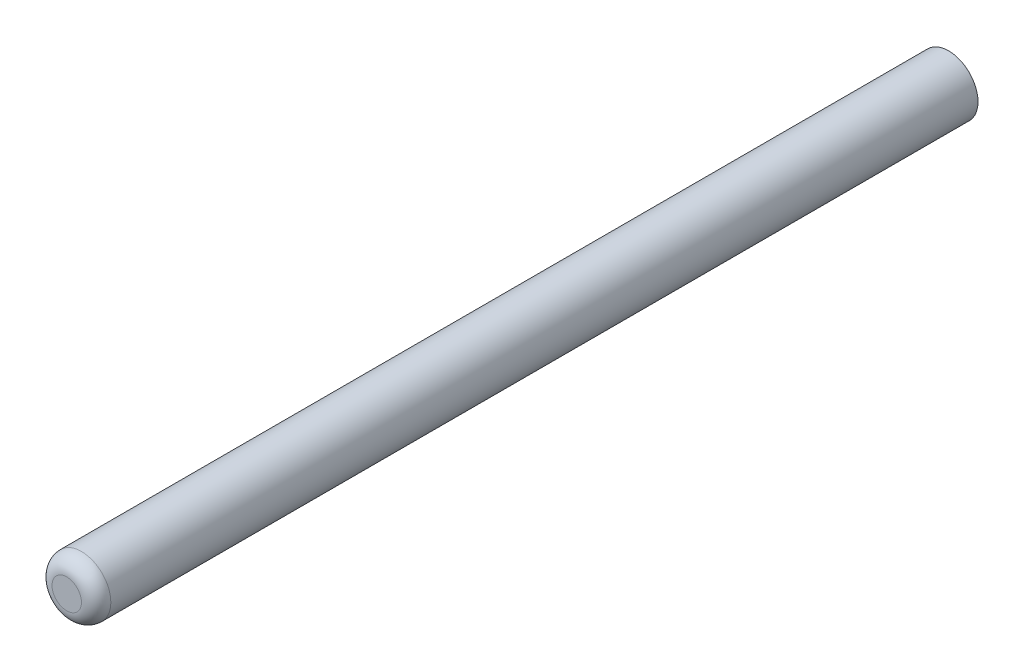
SolidWorks part; units mm, degrees
ref_plane "Front Plane" through (0, 0, 0) normal (0, 0, 1) x (1, 0, 0)
ref_plane "Top Plane" through (0, 0, 0) normal (0, 1, 0) x (1, 0, 0)
ref_plane "Right Plane" through (0, 0, 0) normal (1, 0, 0) x (0, 0, -1)
sketch "Sketch1" plane through (0, 0, 0) normal (0, 0, 1) x (1, 0, 0)
  circle A0 centre (0, 0) radius 10
  dimension "D1" = 20
extrude "Boss-Extrude1" add sketch "Sketch1" along normal blind 300
chamfer "Chamfer1" [suppressed] distance 5 angle 45
fillet "Fillet1" radius 5 1 edges at (10, 0, 300)
